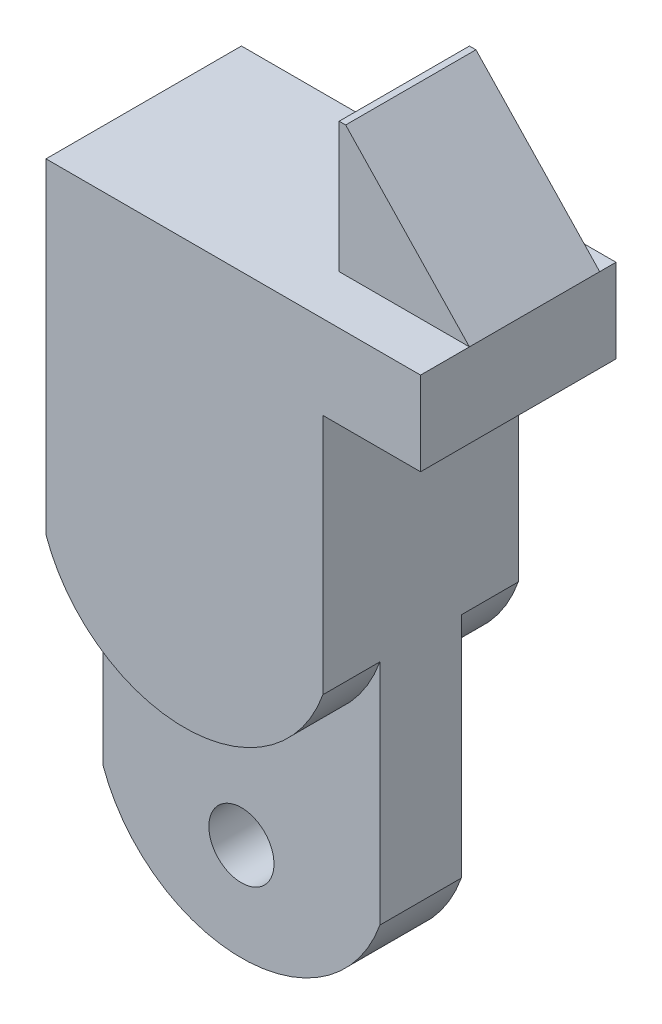
SolidWorks part; units mm, degrees
ref_plane "Plan de face" through (0, 0, 0) normal (0, 0, 1) x (1, 0, 0)
ref_plane "Plan de dessus" through (0, 0, 0) normal (0, 1, 0) x (1, 0, 0)
ref_plane "Plan de droite" through (0, 0, 0) normal (1, 0, 0) x (0, 0, -1)
sketch "Esquisse1" plane through (0, 0, 0) normal (0, 0, 1) x (1, 0, 0)
  line L1 (0, 0) -> (11.5, 0)
  line L2 (0, 0) -> (0, -20)
  line L3 (0, -20) -> (11.5, -20)
  line L4 (11.5, 0) -> (11.5, -20)
  dimension "D1" = 11.5
  dimension "D2" = 20
extrude "Boss.-Extru.2" add sketch "Esquisse1" along normal blind 6
sketch "Esquisse2" plane through (0, 0, 6) normal (0, 0, 1) x (1, 0, 0)
  line L0 (11.5, -20) -> (11.5, 0) construction
  line L1 (11.5, -2.571) -> (8.5, -2.571)
  line L2 (11.5, -2.571) -> (11.5, -20)
  line L3 (11.5, -20) -> (8.5, -20)
  line L4 (8.5, -2.571) -> (8.5, -20)
  line L5 (0, -20) -> (11.5, -20) construction
  dimension "D1" = 3
extrude "Enlèv. mat.-Extru.1" cut sketch "Esquisse2" against normal blind 6
sketch "Esquisse4" plane through (0, 0, 6) normal (0, 0, 1) x (1, 0, 0)
  line L0 (0, -13) -> (8.5, -13) construction
  line L1 (0, 0) -> (0, -20) construction
  line L2 (8.5, -2.571) -> (8.5, -20) construction
  line L3 (4.25, 0) -> (4.25, -20) construction
  line L4 (11.5, 0) -> (0, 0) construction
  line L5 (0, -20) -> (8.5, -20) construction
  line L6 (0, -10) -> (0, -20)
  line L7 (0, -20) -> (8.5, -20)
  line L8 (8.5, -20) -> (8.5, -10)
  arc A0 (0, -10) -> (8.5, -10) centre (4.25, -8.4896) ccw
  dimension "D1" = 13
  dimension "D2" = 3
  dimension "D3" = 4.25
extrude "Enlèv. mat.-Extru.2" cut sketch "Esquisse4" against normal blind 1.75
sketch "Esquisse5" plane through (0, 0, 0) normal (0, 0, -1) x (-1, 0, 0)
  line L0 (-4.25, -20) -> (-4.25, 0) construction
  line L1 (0, -20) -> (-8.5, -20) construction
  line L2 (-11.5, 0) -> (0, 0) construction
  line L3 (-8.5, -13) -> (0, -13) construction
  line L4 (-8.5, -2.571) -> (-8.5, -20) construction
  line L5 (0, 0) -> (0, -20) construction
  arc A0 (0, -10) -> (-8.5, -10) centre (-4.25, -8.4896) cw
  dimension "D1" = 13
  dimension "D2" = 3
  dimension "D3" = 4.25
extrude "Enlèv. mat.-Extru.4" cut sketch "Esquisse5" against normal blind 1.75 and the other way through all
sketch "Esquisse6" plane through (0, 0, 1.75) normal (0, 0, -1) x (-1, 0, 0)
  line L0 (-4.25, -20) -> (-4.25, -13) construction
  line L1 (0, -20) -> (-8.5, -20) construction
  line L2 (-8.5, -17) -> (0, -17) construction
  line L3 (-8.5, -10) -> (-8.5, -20) construction
  line L4 (0, -10) -> (0, -20) construction
  line L5 (-8.5, -17) -> (-8.5, -20)
  line L6 (-8.5, -20) -> (0, -20)
  line L7 (0, -20) -> (0, -17)
  arc A0 (-8.5, -10) -> (0, -10) centre (-4.25, -8.4896) ccw construction
  arc A1 (-8.5, -17) -> (0, -17) centre (-4.25, -15.4896) ccw
  line M1 (0, -20) -> (0, -10)
  line M3 (-8.5, -10) -> (-8.5, -20)
  line M4 (-8.5, -20) -> (0, -20)
  dimension "D1" = 3
extrude "Enlèv. mat.-Extru.5" cut sketch "Esquisse6" against normal blind 2.5 contours A1 M3 M4 | A1 L6 M1
sketch "Esquisse7" plane through (0, 0, 1.75) normal (0, 0, -1) x (-1, 0, 0)
  line L0 (-8.5, -17) -> (0, -17) construction
  line L1 (0, -17) -> (-4.25, -20) construction
  line L2 (-4.25, -20) -> (-4.25, -13) construction
  arc A0 (-8.5, -17) -> (0, -17) centre (-4.25, -15.4896) ccw construction
  arc A1 (-8.5, -10) -> (0, -10) centre (-4.25, -8.4896) ccw construction
  circle A2 centre (-4.25, -17) radius 1
  dimension "D1" = 2
  dimension "D2" = 4
extrude "Enlèv. mat.-Extru.6" cut sketch "Esquisse7" against normal blind 2.5
sketch "Esquisse8" plane through (0, 0, 0) normal (0, 1, 0) x (1, 0, 0)
  line L0 (11.5, -6) -> (11.5, 0) construction
  line L1 (11.5, -0.5) -> (7.5, -0.5)
  line L2 (11.5, -0.5) -> (11.5, -4.5)
  line L3 (11.5, -4.5) -> (7.5, -4.5)
  line L4 (7.5, -0.5) -> (7.5, -4.5)
  dimension "D1" = 0.5
  dimension "D2" = 1.5
  dimension "D3" = 4
extrude "Boss.-Extru.3" add sketch "Esquisse8" along normal blind 4
sketch "Esquisse9" plane through (0, 0, 4.5) normal (0, 0, 1) x (1, 0, 0)
  line L0 (11.5, 4) -> (7.7, 4)
  line L1 (7.5, 4) -> (11.5, 4) construction
  line L2 (7.7, 4) -> (11.5, 0)
  line L3 (11.5, 4) -> (11.5, 0) construction
  line L4 (11.5, 0) -> (11.5, 4)
  dimension "D1" = 3.8
  dimension "D2" = 4
extrude "Enlèv. mat.-Extru.8" cut sketch "Esquisse9" against normal blind 4
